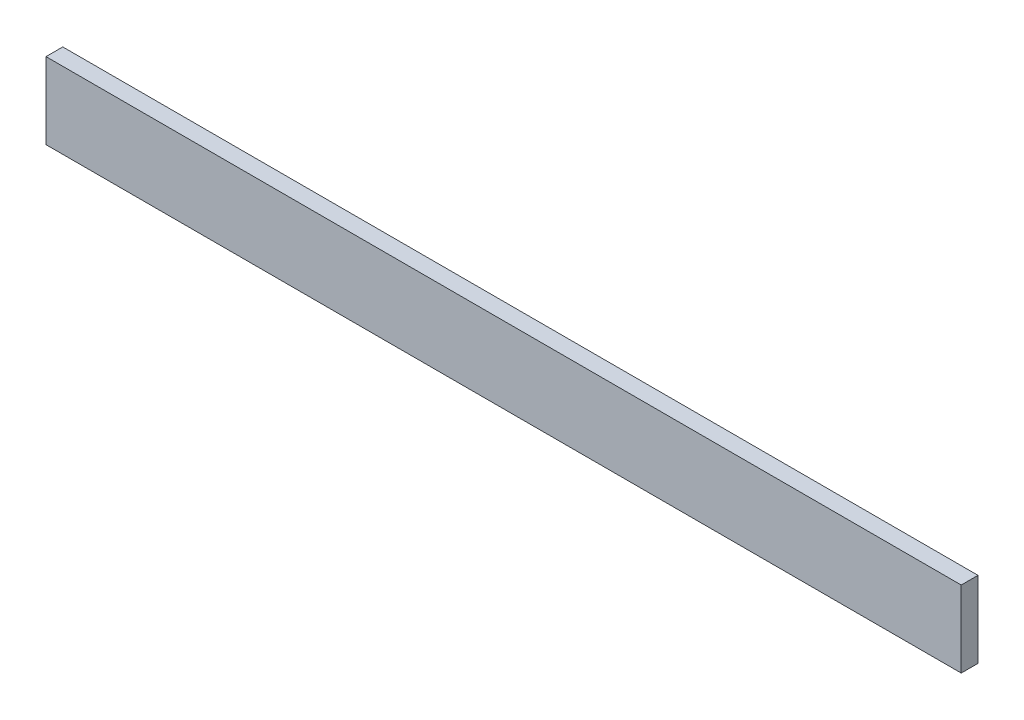
SolidWorks part; units mm, degrees
material "Pine"
ref_plane "Front Plane" through (0, 0, 0) normal (0, 0, 1) x (1, 0, 0)
ref_plane "Top Plane" through (0, 0, 0) normal (0, 1, 0) x (1, 0, 0)
ref_plane "Right Plane" through (0, 0, 0) normal (1, 0, 0) x (0, 0, -1)
sketch "Sketch1" plane through (0, 0, 0) normal (0, 0, 1) x (1, 0, 0)
  line L1 (600, 50) -> (-600, 50)
  line L2 (600, 50) -> (600, -50)
  line L3 (600, -50) -> (-600, -50)
  line L4 (-600, 50) -> (-600, -50)
  point P4 (-600, 0)
  point P5 (0, -50)
  dimension "D1" = 100
  dimension "D2" = 1200
extrude "Boss-Extrude1" add sketch "Sketch1" along normal blind 22
